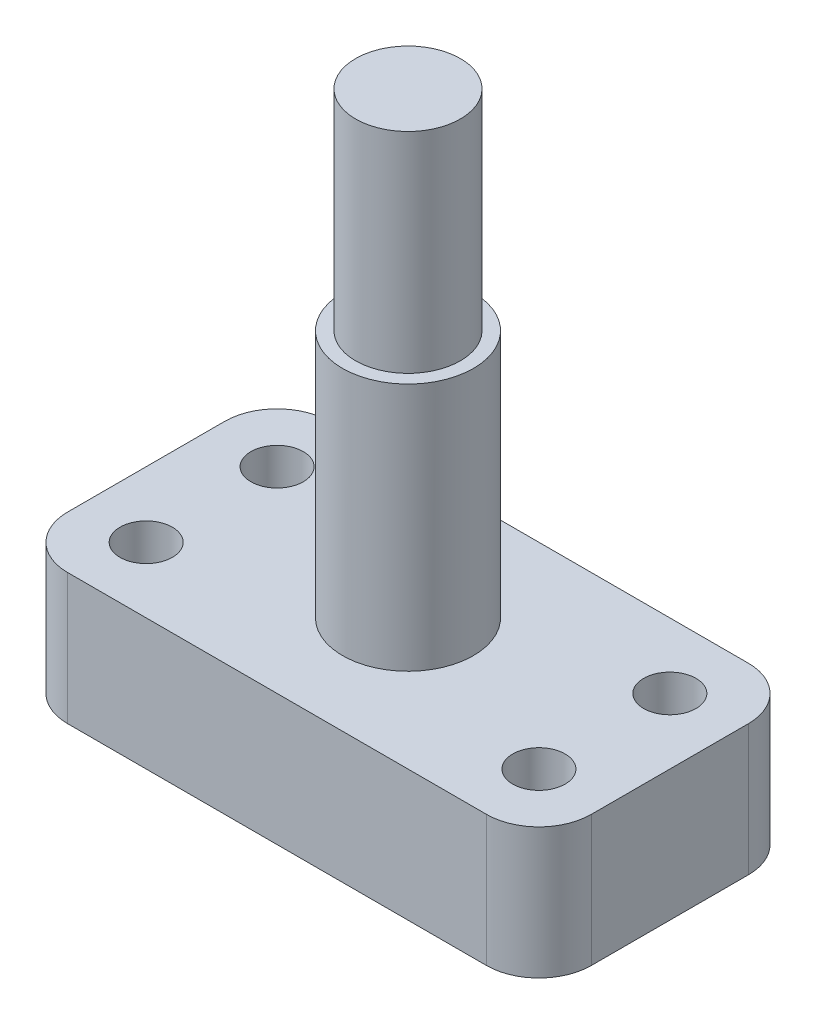
SolidWorks part; units mm, degrees
ref_plane "Front Plane" through (0, 0, 0) normal (0, 0, 1) x (1, 0, 0)
ref_plane "Top Plane" through (0, 0, 0) normal (0, 1, 0) x (1, 0, 0)
ref_plane "Right Plane" through (0, 0, 0) normal (1, 0, 0) x (0, 0, -1)
sketch "Sketch1" plane through (0, 0, 0) normal (0, 1, 0) x (1, 0, 0)
  line L0 (20, 20) -> (20, 0) construction
  line L1 (4, 0) -> (36, 0)
  line L2 (0, 4) -> (0, 16)
  line L3 (4, 20) -> (36, 20)
  line L4 (40, 4) -> (40, 16)
  line L5 (0, 10) -> (20, 10) construction
  arc A0 (36, 20) -> (40, 16) centre (36, 16) cw
  arc A1 (36, 0) -> (40, 4) centre (36, 4) ccw
  arc A2 (4, 0) -> (0, 4) centre (4, 4) cw
  arc A3 (0, 16) -> (4, 20) centre (4, 16) cw
  circle A4 centre (5, 15) radius 2
  circle A5 centre (5, 5) radius 2
  circle A6 centre (35, 5) radius 2
  circle A7 centre (35, 15) radius 2
  point P9 (40, 0)
  point P12 (0, 0)
  point P15 (0, 20)
  dimension "D3" = 4
  dimension "D5" = 4
  dimension "D1" = 40
  dimension "D2" = 20
  dimension "D4" = 5
  dimension "D6" = 5
extrude "Boss-Extrude1" add sketch "Sketch1" along normal blind 10
sketch "Sketch2" plane through (0, 10, 0) normal (0, 1, 0) x (1, 0, 0)
  circle A0 centre (20, 10) radius 5
  dimension "D1" = 10
extrude "Boss-Extrude2" add sketch "Sketch2" along normal blind 19
sketch "Sketch3" plane through (0, 29, 0) normal (0, 1, 0) x (1, 0, 0)
  circle A0 centre (20, 10) radius 4
  dimension "D1" = 8
extrude "Boss-Extrude3" add sketch "Sketch3" along normal blind 16
